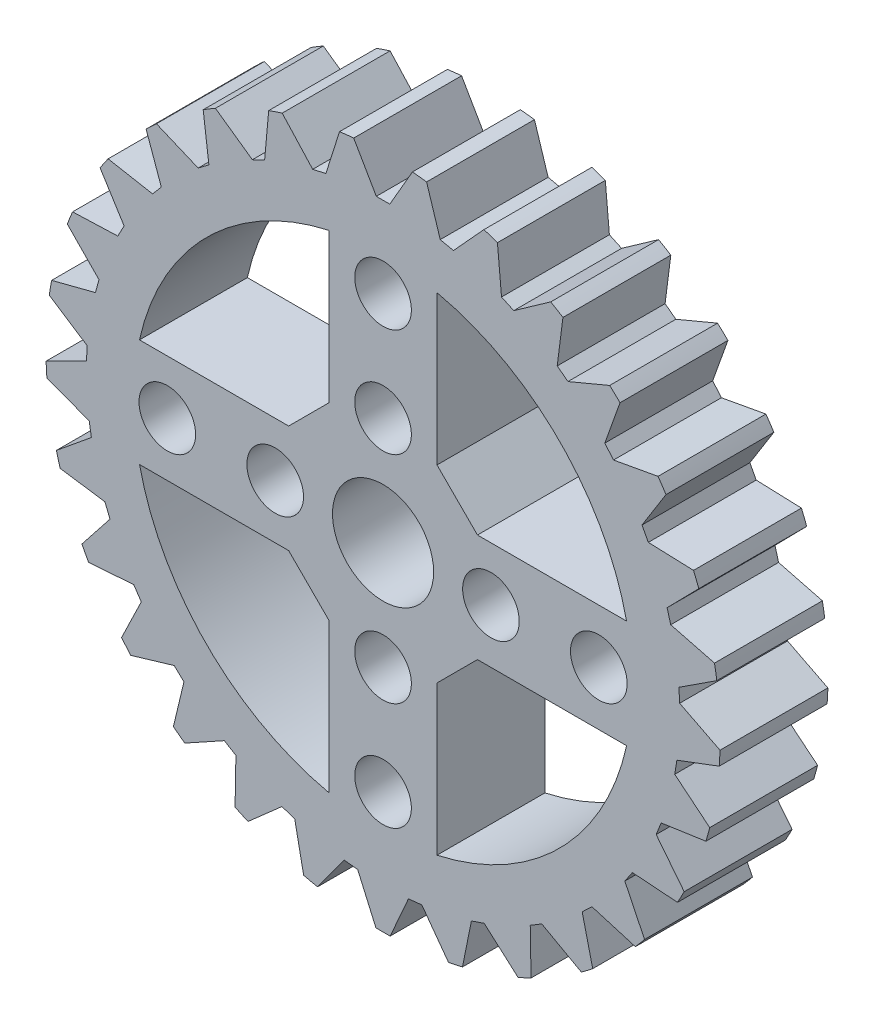
SolidWorks part; units mm, degrees
ref_plane "Front Plane" through (0, 0, 0) normal (0, 0, 1) x (1, 0, 0)
ref_plane "Top Plane" through (0, 0, 0) normal (0, 1, 0) x (1, 0, 0)
ref_plane "Right Plane" through (0, 0, 0) normal (1, 0, 0) x (0, 0, -1)
sketch "Sketch1" plane through (0, 0, 0) normal (0, 0, 1) x (1, 0, 0)
  line L0 (0, 25) -> (0, -25) construction
  line L1 (-25, 0) -> (25, 0) construction
  line L2 (-4, 18.0624) -> (-4, -18.0624)
  line L3 (4, 18.0624) -> (4, -18.0624)
  line L4 (-18.0624, 4) -> (18.0624, 4)
  line L5 (-18.0624, -4) -> (18.0624, -4)
  circle A0 centre (0, 0) radius 25
  circle A1 centre (0, 0) radius 18.5
  dimension "D1" = 50
  dimension "D2" = 6.5
  dimension "D3" = 4
  dimension "D4" = 4
  dimension "D5" = 4
  dimension "D6" = 4
extrude "Boss-Extrude1" add sketch "Sketch1" along normal blind 8 contours A0 A1 | L5 A1 L4 L3 | L2 A1 L3 L5 | L2 L5 L3 L4 | L4 A1 L5 L2 | L3 A1 L2 L4
chamfer "Chamfer1" distance 3 angle 45 4 edges at (-4, 4, 4) (4, 4, 4) (4, -4, 4) (-4, -4, 4)
sketch "Sketch2" plane through (0, 0, 8) normal (0, 0, 1) x (1, 0, 0)
  line L0 (-25, 0) -> (25, 0) construction
  circle A0 centre (0, 0) radius 3.75
  circle A1 centre (0, 0) radius 25 construction
  circle A2 centre (-8, 0) radius 2.1
  circle A4 centre (-16, 0) radius 2.1
  dimension "D1" = 7.5
  dimension "D2" = 4.2
  dimension "D3" = 8
  dimension "D4" = 8
extrude "Cut-Extrude1" cut sketch "Sketch2" against normal blind 10
sketch "Sketch3" plane through (0, 0, 8) normal (0, 0, 1) x (1, 0, 0)
  line L0 (-2.8094, 26) -> (-0.5, 22)
  line L1 (-0.5, 22) -> (0.5, 22)
  line L2 (0.5, 22) -> (2.8094, 26)
  line L3 (-2.8094, 26) -> (2.8094, 26)
  line L4 (0, 22) -> (0, 0) construction
  circle A1 centre (0, 0) radius 25 construction
  dimension "D5" = 22
  dimension "D1" = 120
  dimension "D2" = 120
  dimension "D3" = 4
  dimension "D4" = 1
extrude "Cut-Extrude4" cut sketch "Sketch3" against normal blind 10
pattern_circular "CirPattern1" count 29 over 360 about axis through (0, 0, 0) along (0, 0, 1) of "Cut-Extrude4"
pattern_circular "CirPattern2" count 4 over 360 about axis through (0, 0, 0) along (0, 0, 1) of "Cut-Extrude1"
